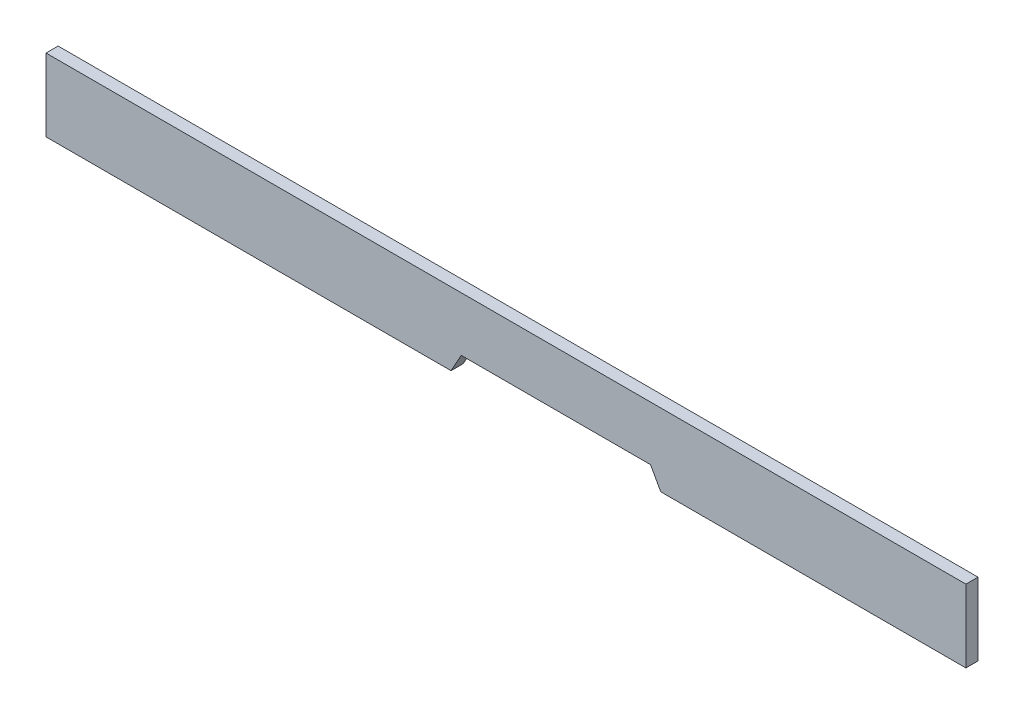
SolidWorks part; units mm, degrees
ref_plane "Front" through (0, 0, 0) normal (0, 0, 1) x (1, 0, 0)
ref_plane "Top" through (0, 0, 0) normal (0, 1, 0) x (1, 0, 0)
ref_plane "Right" through (0, 0, 0) normal (1, 0, 0) x (0, 0, -1)
sketch "Sketch1" plane through (0, 0, 0) normal (0, 0, 1) x (1, 0, 0)
  line L1 (-60.325, -4.7625) -> (60.325, -4.7625)
  line L2 (-60.325, -4.7625) -> (-60.325, 4.7625)
  line L3 (-60.325, 4.7625) -> (60.325, 4.7625)
  line L4 (60.325, -4.7625) -> (60.325, 4.7625)
  line L5 (-60.325, -4.7625) -> (60.325, 4.7625) construction
  line L6 (-60.325, 4.7625) -> (60.325, -4.7625) construction
  point P0 (0, 0)
  dimension "D1" = 120.65
  dimension "D2" = 9.525
extrude "Boss-Extrude1" add sketch "Sketch1" along normal mid plane 1.5875
sketch "Sketch2" plane through (0, 0, 0.7937) normal (0, 0, 1) x (1, 0, 0)
  line L0 (-7.2022, -4.7625) -> (-5.8557, -2.3495)
  line L1 (-60.325, -4.7625) -> (60.325, -4.7625) construction
  line L2 (-5.8557, -2.3495) -> (18.9604, -2.3495)
  line L3 (18.9604, -2.3495) -> (20.3069, -4.7625)
  line L4 (-7.2022, -4.7625) -> (20.3069, -4.7625)
  dimension "D1" = 2.413
extrude "Cut-Extrude1" cut sketch "Sketch2" against normal through all
